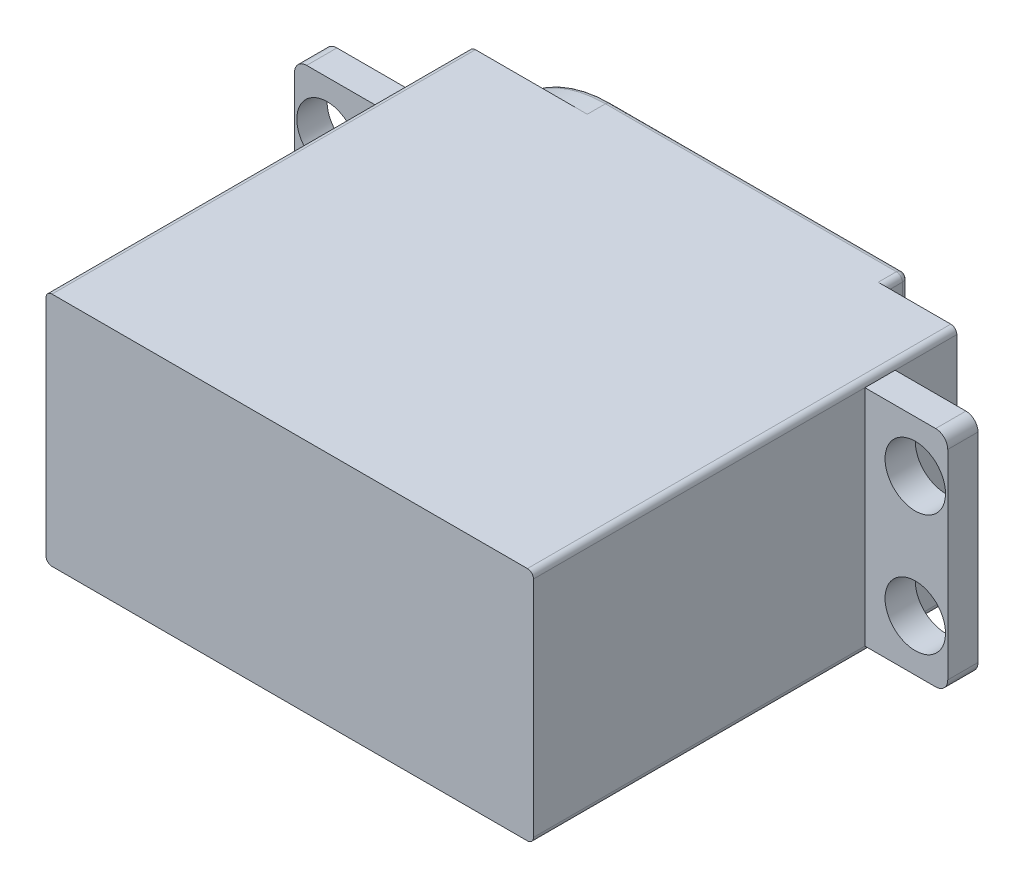
SolidWorks part; units mm, degrees
ref_plane "前视基准面" through (0, 0, 0) normal (0, 0, 1) x (1, 0, 0)
ref_plane "上视基准面" through (0, 0, 0) normal (0, 1, 0) x (1, 0, 0)
ref_plane "右视基准面" through (0, 0, 0) normal (1, 0, 0) x (0, 0, -1)
sketch "草图1" plane through (0, 0, 0) normal (0, 0, 1) x (1, 0, 0)
  line L1 (-8.1359, 0.7134) -> (31.1641, 0.7134)
  line L2 (-8.6359, 0.2134) -> (-8.6359, -18.2866)
  line L3 (-8.1359, -18.7866) -> (31.1641, -18.7866)
  line L4 (31.6641, 0.2134) -> (31.6641, -18.2866)
  arc A0 (31.6641, 0.2134) -> (31.1641, 0.7134) centre (31.1641, 0.2134) ccw
  arc A1 (31.1641, -18.7866) -> (31.6641, -18.2866) centre (31.1641, -18.2866) ccw
  arc A2 (-8.6359, 0.2134) -> (-8.1359, 0.7134) centre (-8.1359, 0.2134) cw
  arc A3 (-8.1359, -18.7866) -> (-8.6359, -18.2866) centre (-8.1359, -18.2866) cw
  point P6 (31.6641, 0.7134)
  point P9 (31.6641, -18.7866)
  point P14 (-8.6359, -18.7866)
  dimension "D3" = 0.5
  dimension "D4" = 0.5
  dimension "D5" = 0.5
  dimension "D6" = 0.5
  dimension "D1" = 19.5
  dimension "D2" = 40.3
extrude "凸台-拉伸1" add sketch "草图1" along normal blind 35
sketch "草图2" plane through (0, 0, 0) normal (0, 0, -1) x (-1, 0, 0)
  line L0 (-37.7746, -9.0366) -> (18.5796, -9.0366) construction
  line L1 (-31.6641, -18.2866) -> (-31.6641, 0.2134) construction
  line L2 (8.1359, -18.7866) -> (-31.1641, -18.7866) construction
  line L3 (-25.6641, -18.2866) -> (-25.6641, 0.2134)
  line L4 (-31.1641, 0.7134) -> (8.1359, 0.7134) construction
  line L5 (-25.1641, 0.7134) -> (-1.1141, 0.7134)
  line L6 (-25.1641, -18.7866) -> (-1.1141, -18.7866)
  line L7 (8.6359, 0.2134) -> (8.6359, -18.2866) construction
  line L8 (-25.6641, 0.7134) -> (-25.6759, 0.6407)
  arc A0 (-1.1141, -18.7866) -> (-1.1141, 0.7134) centre (-1.1141, -9.0366) ccw
  arc A1 (-25.6641, 0.2134) -> (-25.1641, 0.7134) centre (-25.1641, 0.2134) cw
  arc A2 (-25.1641, -18.7866) -> (-25.6641, -18.2866) centre (-25.1641, -18.2866) cw
  point P19 (-25.6641, -9.0366)
  point P23 (-25.6641, -18.7866)
  dimension "D2" = 0.5
  dimension "D4" = 0.5
  dimension "D1" = 9.75
  dimension "D3" = 9.75
extrude "凸台-拉伸2" add sketch "草图2" along normal up to surface (37 mm away) from offset 2 contours L3 A1 L5 A0 L6 A2
sketch "草图10" plane through (0, 0, -2) normal (0, 0, -1) x (-1, 0, 0)
  line L0 (-40.5387, -9.0366) -> (19.3951, -9.0366) construction
  line L1 (-25.6641, -18.2866) -> (-25.6641, 0.2134) construction
  line L2 (-25.1641, -18.7866) -> (-31.1641, -18.7866) construction
  circle A2 centre (-1.6641, -9.0366) radius 7
  dimension "D5" = 14
  dimension "D1" = 9.75
  dimension "D4" = 10.3
extrude "凸台-拉伸6" add sketch "草图10" along normal blind 2
sketch "草图15" plane through (0, 0, -4) normal (0, 0, -1) x (-1, 0, 0)
  circle A0 centre (-1.6641, -9.0366) radius 2.9
extrude "凸台-拉伸7" add sketch "草图15" along normal blind 4
sketch "草图16" plane through (0, 0, -8) normal (0, 0, -1) x (-1, 0, 0)
  circle A0 centre (-1.6641, -9.0366) radius 1.5
extrude "切除-拉伸1" cut sketch "草图16" against normal blind 4
sketch "草图17" plane through (31.6641, 0, 0) normal (1, 0, 0) x (0, 0, -1)
  line L0 (-35, -18.2866) -> (0, -18.2866) construction
  line L1 (-35, 0.2134) -> (0, 0.2134) construction
  line L2 (-5.1, -18.2866) -> (-7.6, -18.2866)
  line L3 (-5.1, -18.2866) -> (-5.1, 0.2134)
  line L4 (-5.1, 0.2134) -> (-7.6, 0.2134)
  line L5 (-7.6, -18.2866) -> (-7.6, 0.2134)
  line L6 (0, 0.2134) -> (0, -18.2866) construction
  dimension "D1" = 2.5
  dimension "D2" = 5.1
extrude "凸台-拉伸9" add sketch "草图17" along normal blind 6.85
ref_plane "基准面2" through (11.5141, 0, 0) normal (-1, 0, 0) x (0, 0, 1)
sketch "草图19" plane through (0, 0, 5.1) normal (0, 0, -1) x (-1, 0, 0)
  line L0 (-41.5912, -9.0366) -> (15.2695, -9.0366) construction
  line L1 (-11.5141, -28.2902) -> (-11.5141, 5.0374) construction
  line L2 (-38.5141, -18.2866) -> (-38.5141, 0.2134) construction
  line L3 (-25.1641, -18.7866) -> (-1.1141, -18.7866) construction
  line L4 (-31.6641, -18.2866) -> (-31.6641, 0.2134) construction
  line L5 (-38.5141, -18.2866) -> (-31.6641, -18.2866) construction
  circle A0 centre (-35.8291, -4.0366) radius 2.5
  circle A1 centre (-35.8291, -14.0366) radius 2.5
  dimension "D1" = 10
  dimension "D2" = 5
  dimension "D3" = 20.15
  dimension "D4" = 24.315
  dimension "D5" = 4.25
extrude "切除-拉伸2" cut sketch "草图19" against normal through all
mirror "镜向3" about plane through (11.5141, 0, 0) normal (-1, 0, 0) of "切除-拉伸2", "凸台-拉伸9"
fillet "圆角1" radius 1 1 edges at (38.5141, 0.2134, 6.35)
fillet "圆角2" radius 1 1 edges at (38.5141, -18.2866, 6.35)
fillet "圆角3" radius 1 1 edges at (-15.4859, 0.2134, 6.35)
fillet "圆角4" radius 1 1 edges at (-15.4859, -18.2866, 6.35)
fillet "圆角5" radius 0.5 1 edges at (-1.2359, -9.0366, -8)
fillet "圆角6" radius 0.5 1 edges at (-5.3359, -9.0366, -4)
fillet "圆角7" radius 0.5 6 edges at (13.1391, 0.7134, -2) (25.5177, 0.5669, -2) (25.6641, -9.0366, -2) (25.5177, -18.6402, -2) (13.1391, -18.7866, -2) (-8.6359, -9.0366, -2)
